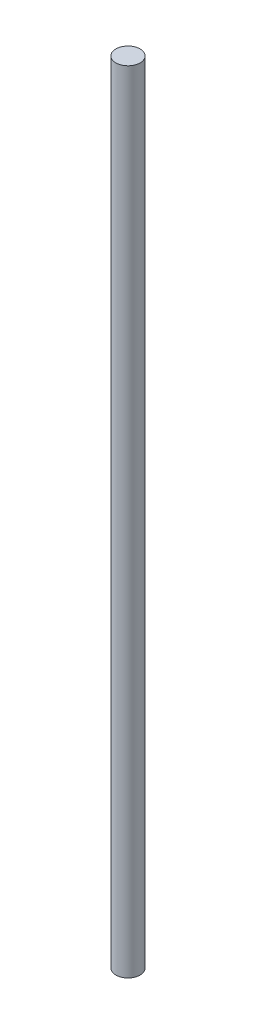
SolidWorks part; units mm, degrees
material "Alumina"
ref_plane "Front Plane" through (0, 0, 0) normal (0, 0, 1) x (1, 0, 0)
ref_plane "Top Plane" through (0, 0, 0) normal (0, 1, 0) x (1, 0, 0)
ref_plane "Right Plane" through (0, 0, 0) normal (1, 0, 0) x (0, 0, -1)
sketch "Sketch1" plane through (0, 0, 0) normal (0, 1, 0) x (1, 0, 0)
  circle A0 centre (0, 0) radius 5.842
extrude "Boss-Extrude1" add sketch "Sketch1" along normal blind 381
